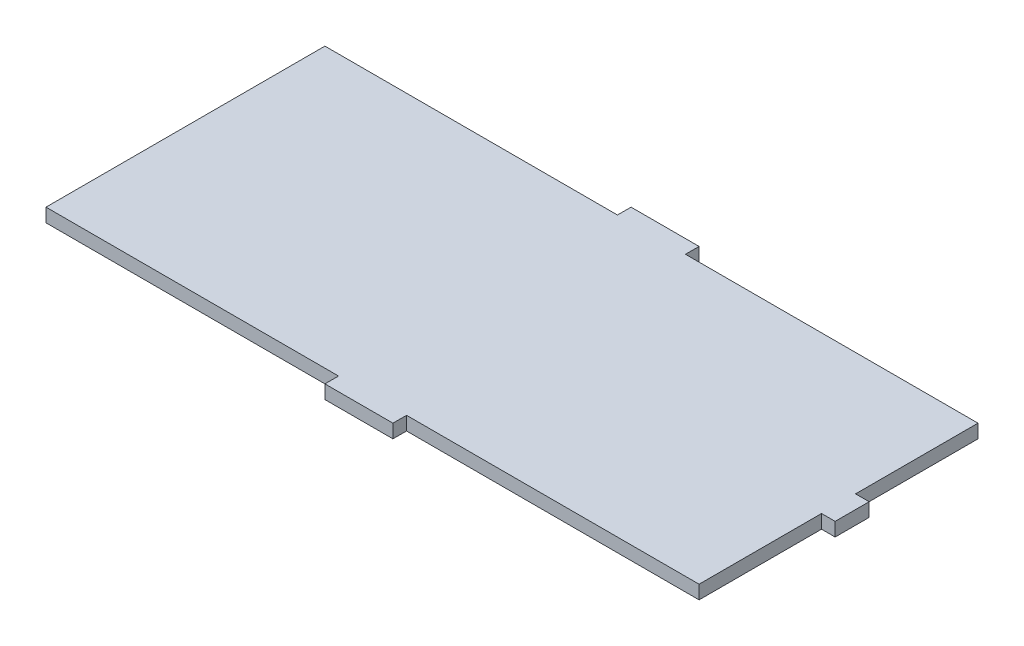
SolidWorks part; units mm, degrees
ref_plane "Front Plane" through (0, 0, 0) normal (0, 0, 1) x (1, 0, 0)
ref_plane "Top Plane" through (0, 0, 0) normal (0, 1, 0) x (1, 0, 0)
ref_plane "Right Plane" through (0, 0, 0) normal (1, 0, 0) x (0, 0, -1)
sketch "Sketch1" plane through (0, 0, 0) normal (0, 1, 0) x (1, 0, 0)
  line L16 (0, 0) -> (43, 0)
  line L17 (43, 0) -> (43, -2)
  line L18 (43, -2) -> (53, -2)
  line L19 (53, -2) -> (53, 0)
  line L20 (53, 0) -> (96, 0)
  line L21 (96, 0) -> (96, 18)
  line L22 (96, 18) -> (98, 18)
  line L23 (98, 18) -> (98, 23)
  line L24 (98, 23) -> (96, 23)
  line L25 (96, 23) -> (96, 41)
  line L26 (96, 41) -> (53, 41)
  line L27 (53, 41) -> (53, 43)
  line L28 (53, 43) -> (43, 43)
  line L29 (43, 43) -> (43, 41)
  line L30 (43, 41) -> (0, 41)
  line L31 (0, 41) -> (0, 0)
  dimension "D1" = 2
  dimension "D2" = 96
  dimension "D3" = 43
  dimension "D4" = 10
  dimension "D5" = 41
  dimension "D6" = 5
extrude "Boss-Extrude1" add sketch "Sketch1" along normal blind 2
